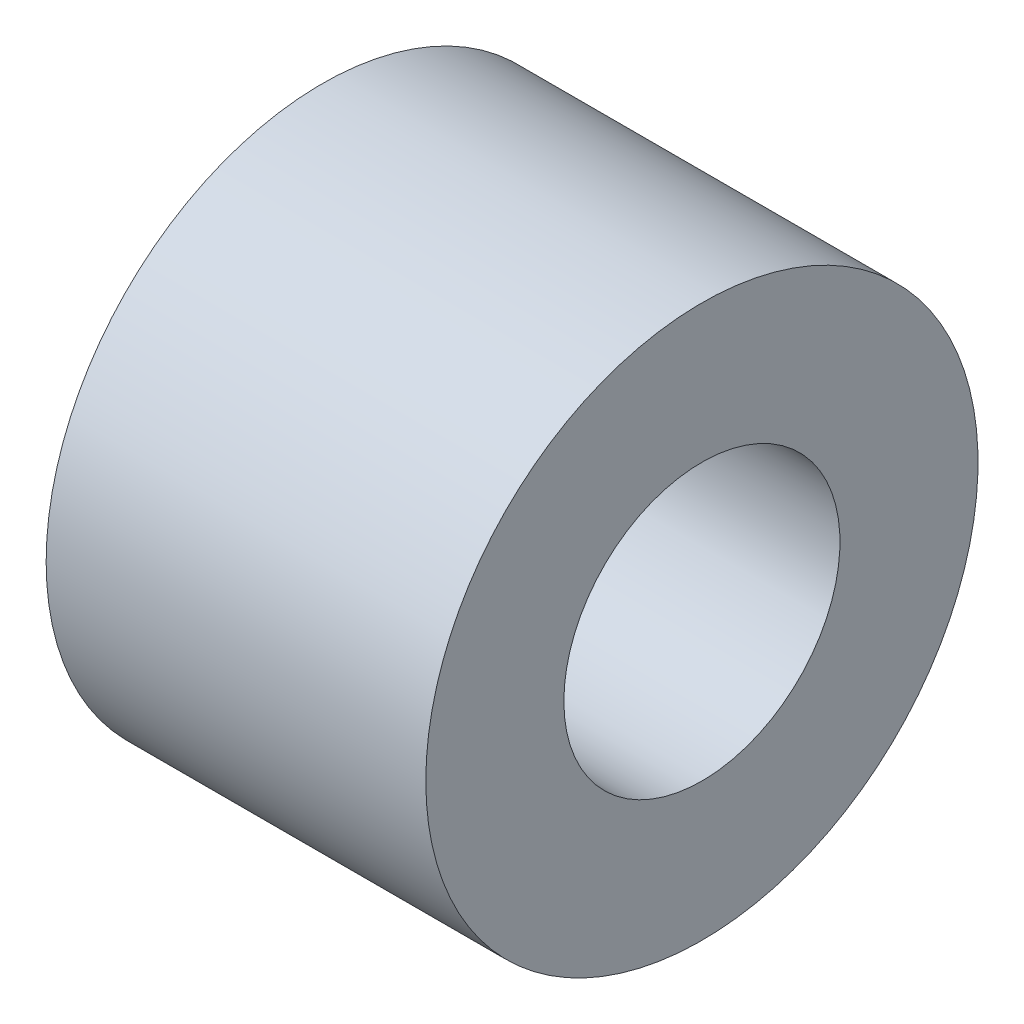
SolidWorks part; units mm, degrees
ref_plane "Front Plane" through (0, 0, 0) normal (0, 0, 1) x (1, 0, 0)
ref_plane "Top Plane" through (0, 0, 0) normal (0, 1, 0) x (1, 0, 0)
ref_plane "Right Plane" through (0, 0, 0) normal (1, 0, 0) x (0, 0, -1)
sketch "Sketch1" plane through (0, 0, 0) normal (0, 0, 1) x (1, 0, 0)
  line L0 (0, 0) -> (5.5, 0) construction
  line L1 (0, -2) -> (0, -4)
  line L2 (0, -4) -> (5.5, -4)
  line L3 (5.5, -4) -> (5.5, -2)
  line L4 (5.5, -2) -> (0, -2)
  dimension "D1" = 2
  dimension "D2" = 4
  dimension "D3" = 5.5
revolve "Revolve1" add sketch "Sketch1" angle 360 about L0
